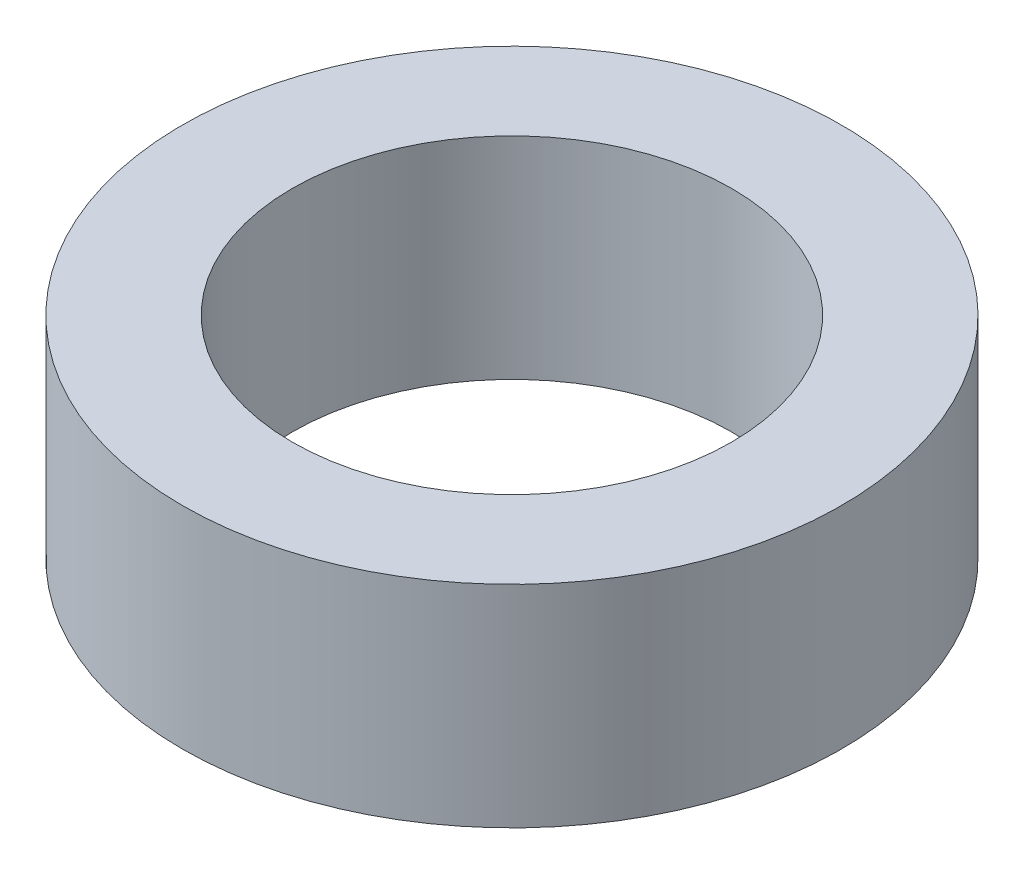
SolidWorks part; units mm, degrees
material "PVC Rigid"
ref_plane "Front Plane" through (0, 0, 0) normal (0, 0, 1) x (1, 0, 0)
ref_plane "Top Plane" through (0, 0, 0) normal (0, 1, 0) x (1, 0, 0)
ref_plane "Right Plane" through (0, 0, 0) normal (1, 0, 0) x (0, 0, -1)
sketch "Sketch1" plane through (0, 0, 0) normal (0, 1, 0) x (1, 0, 0)
  circle A0 centre (0, 0) radius 9.525
  circle A1 centre (0, 0) radius 6.35
  dimension "D1" = 19.05
  dimension "D2" = 12.7
extrude "Boss-Extrude1" add sketch "Sketch1" along normal blind 6.096
